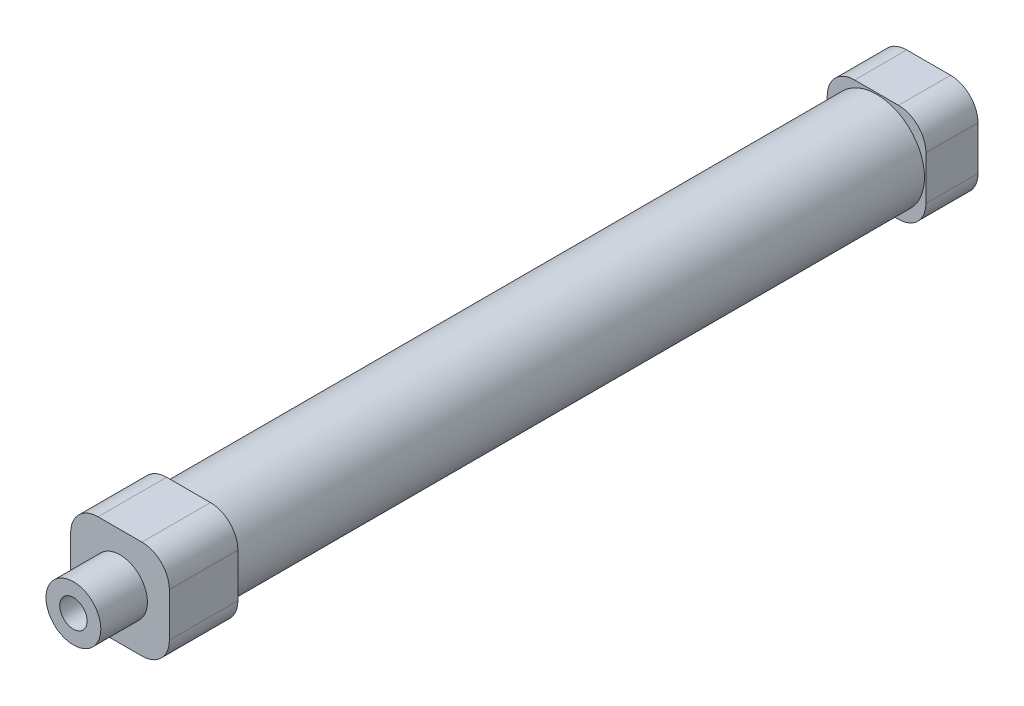
SolidWorks part; units mm, degrees
material "6063-T6"
ref_plane "前视基准面" through (0, 0, 0) normal (0, 0, 1) x (1, 0, 0)
ref_plane "上视基准面" through (0, 0, 0) normal (0, 1, 0) x (1, 0, 0)
ref_plane "右视基准面" through (0, 0, 0) normal (1, 0, 0) x (0, 0, -1)
sketch "草图1" plane through (0, 0, 0) normal (0, 0, 1) x (1, 0, 0)
  line L1 (-9, 9) -> (9, 9)
  line L2 (-9, 9) -> (-9, -9)
  line L3 (-9, -9) -> (9, -9)
  line L4 (9, 9) -> (9, -9)
  line L5 (-9, 9) -> (9, -9) construction
  line L6 (-9, -9) -> (9, 9) construction
  point P0 (0, 0)
  dimension "D1" = 18
  dimension "D2" = 18
extrude "凸台-拉伸1" add sketch "草图1" along normal blind 9.5
sketch "草图2" plane through (0, 0, 9.5) normal (0, 0, 1) x (1, 0, 0)
  line L0 (0, 9) -> (0, -9) construction
  line L1 (9, 9) -> (-9, 9) construction
  line L2 (-9, -9) -> (9, -9) construction
  circle A0 centre (0, 0) radius 8.75
  dimension "D1" = 17.5
extrude "凸台-拉伸2" add sketch "草图2" along normal blind 125.5
sketch "草图3" plane through (0, 0, 135) normal (0, 0, 1) x (1, 0, 0)
  line L1 (-9, -9) -> (9, -9)
  line L2 (-9, -9) -> (-9, 9)
  line L3 (-9, 9) -> (9, 9)
  line L4 (9, -9) -> (9, 9)
  line L5 (-9, -9) -> (9, 9) construction
  line L6 (-9, 9) -> (9, -9) construction
  point P0 (0, 0)
extrude "凸台-拉伸3" add sketch "草图3" along normal blind 12.5
sketch "草图4" plane through (0, 0, 147.5) normal (0, 0, 1) x (1, 0, 0)
  circle A0 centre (0, 0) radius 5
  dimension "D1" = 10
extrude "凸台-拉伸4" add sketch "草图4" along normal blind 8.5
cosmetic thread "装饰螺纹线1" parameters "D2"=6.941
sketch "草图5" plane through (0, 0, 156) normal (0, 0, 1) x (1, 0, 0)
  circle A0 centre (0, 0) radius 2.5
  dimension "D1" = 5
extrude "切除-拉伸1" cut sketch "草图5" against normal offset from surface (155 mm away) 1 up to face at (0, 0, 0)
fillet "圆角1" radius 5 8 edges at (-9, 9, 141.25) (-9, -9, 141.25) (9, -9, 4.75) (9, -9, 141.25) (9, 9, 4.75) (9, 9, 141.25) (-9, 9, 4.75) (-9, -9, 4.75)
sketch "草图6" plane through (0, -9, 0) normal (0, -1, 0) x (1, 0, 0)
  line L0 (4, 4.75) -> (-4, 4.75) construction
  line L1 (4, 0) -> (4, 9.5) construction
  line L2 (-4, 9.5) -> (-4, 0) construction
  line L3 (-4, 9.5) -> (4, 9.5) construction
  line L4 (4, 139.75) -> (-4, 139.75) construction
  line L5 (4, 135) -> (4, 147.5) construction
  line L6 (-4, 147.5) -> (-4, 135) construction
  line L8 (-4, 135) -> (4, 135) construction
  circle A0 centre (0, 4.75) radius 2.5
  circle A1 centre (0, 139.75) radius 2.5
  dimension "D2" = 5
  dimension "D4" = 5
  dimension "D1" = 4.75
  dimension "D3" = 4.75
extrude "切除-拉伸2" cut sketch "草图6" against normal up to surface (9 mm away) up to plane "上视基准面"
